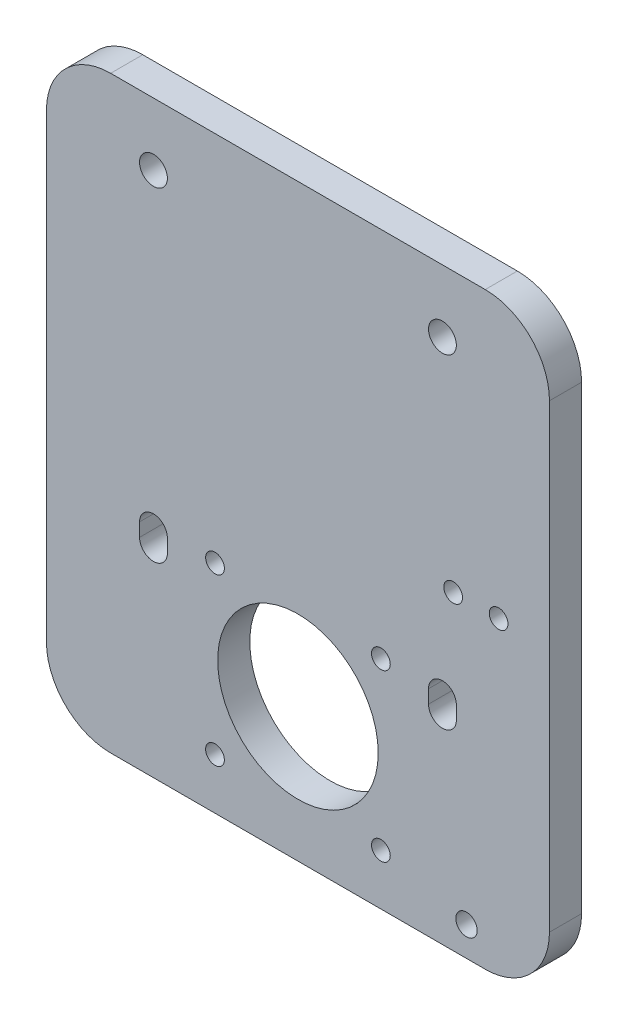
SolidWorks part; units mm, degrees
material "Polycarbonate (PC)"
ref_plane "Спереди" through (0, 0, 0) normal (0, 0, 1) x (1, 0, 0)
ref_plane "Сверху" through (0, 0, 0) normal (0, 1, 0) x (1, 0, 0)
ref_plane "Справа" through (0, 0, 0) normal (1, 0, 0) x (0, 0, -1)
sketch "Model" plane through (0, 0, 0) normal (0, 0, 1) x (1, 0, 0)
  line L4 (-22.7195, 98.3) -> (-31.6357, 98.3) construction
  line L5 (-27, 102.2644) -> (-27, 93.0751) construction
  line L24 (-27, 44.8397) -> (-27, 32.6753) construction
  line L25 (-29.6, 40.1) -> (-29.6, 37.6)
  line L26 (-24.4, 37.6) -> (-24.4, 40.1)
  line L27 (-24.4, 40.1) -> (-24.4, 37.6)
  line L28 (-29.6, 37.6) -> (-29.6, 40.1)
  line L156 (-18.8648, 25) -> (20.0371, 25) construction
  line L159 (27, 44.8397) -> (27, 32.6753) construction
  line L160 (47, 98) -> (47, 12)
  line L165 (27, 102.2644) -> (27, 93.0751) construction
  line L166 (22.7195, 98.3) -> (31.6357, 98.3) construction
  line L167 (35, 0) -> (-35, 0)
  line L174 (-47, 12) -> (-47, 98)
  line L181 (-35, 110) -> (35, 110)
  line L955 (29.6, 37.6) -> (29.6, 40.1)
  line L968 (24.4, 40.1) -> (24.4, 37.6)
  line L1360 (24.4, 37.6) -> (24.4, 40.1)
  line L1373 (29.6, 40.1) -> (29.6, 37.6)
  line L1604 (0, -6.1891) -> (0, 116.9068) construction
  arc A0 (35, 110) -> (47, 98) centre (35, 98) cw
  arc A1 (47, 12) -> (35, 0) centre (35, 12) cw
  arc A2 (-47, 12) -> (-35, 0) centre (-35, 12) ccw
  arc A3 (-47, 98) -> (-35, 110) centre (-35, 98) cw
  circle A8 centre (0, 25) radius 15
  arc A9 (24.4, 40.1) -> (29.6, 40.1) centre (27, 40.1) cw
  arc A10 (24.4, 37.6) -> (29.6, 37.6) centre (27, 37.6) ccw
  circle A19 centre (27, 98.3) radius 2.6
  circle A22 centre (-27, 98.3) radius 2.6
  arc A29 (-24.4, 37.6) -> (-29.6, 37.6) centre (-27, 37.6) cw
  arc A30 (-24.4, 40.1) -> (-29.6, 40.1) centre (-27, 40.1) ccw
  dimension "D1" = 12
  dimension "D12" = 30
  dimension "D15" = 2.6
  dimension "D38" = 5.2
  dimension "D3" = 110
  dimension "D4" = 25
  dimension "D6" = 40.1
  dimension "D7" = 94
  dimension "D8" = 54
  dimension "D13" = 5.2
  dimension "D14" = 2.5
  dimension "D36" = 58.2
extrude "Base" add sketch "Model" along normal blind 6
sketch "Sketch2" plane through (0, 0, 6) normal (0, 0, 1) x (1, 0, 0)
  line L0 (35, 0) -> (-35, 0) construction
  line L1 (47, 98) -> (47, 12) construction
  circle A0 centre (31.5, 5.5) radius 2
  dimension "D1" = 4
  dimension "D2" = 5.5
  dimension "D3" = 15.5
extrude "CableTieMount" cut sketch "Sketch2" against normal through all
hole_wizard "Ø3.5 (3.5) StepperMount" positions "Sketch3" profile "Sketch4" hole size "Ø3.5" standard "ANSI Metric" end condition through all
sketch "Sketch3" plane through (0, 0, 6) normal (0, 0, 1) x (1, 0, 0)
  line L0 (0, 0) -> (0, 14.3141) construction
  line L4 (35, 0) -> (-35, 0) construction
  point P0 (-15.5, 40.5)
  point P2 (-15.5, 9.5)
  point P4 (15.5, 9.5)
  point P6 (15.5, 40.5)
  dimension "D1" = 31
  dimension "D2" = 31
  dimension "D3" = 9.5
sketch "Sketch4" plane through (-15.5, 40.5, 6) normal (1, 0, 0) x (0, -1, 0)
  line L0 (0, 0) -> (0, 6)
  line L1 (0, 6) -> (1.75, 6)
  line L2 (1.75, 6) -> (1.75, 0)
  line L5 (1.75, 0) -> (0, 0)
  line L11 (0, -6.35) -> (0, 107.95) construction
  dimension "Thru Hole Dia." = 3.5
  dimension "Thru Hole Depth" = 6
hole_wizard "Ø3.5 (3.5) CableChainMount" positions "Sketch5" profile "Sketch6" hole size "Ø3.5" standard "ANSI Metric" end condition through all
sketch "Sketch5" plane through (0, 0, 0) normal (0, 0, -1) x (-1, 0, 0)
  line L0 (-47, 98) -> (-47, 12) construction
  line L1 (-35, 0) -> (35, 0) construction
  point P0 (-37.5, 58)
  point P2 (-29, 58)
  dimension "D1" = 9.5
  dimension "D2" = 8.5
  dimension "D3" = 58
sketch "Sketch6" plane through (37.5, 58, 0) normal (1, 0, 0) x (0, 1, 0)
  line L0 (0, 0) -> (0, 6)
  line L1 (0, 6) -> (1.75, 6)
  line L2 (1.75, 6) -> (1.75, 0)
  line L5 (1.75, 0) -> (0, 0)
  line L11 (0, -6.35) -> (0, 107.95) construction
  dimension "Thru Hole Dia." = 3.5
  dimension "Thru Hole Depth" = 6
